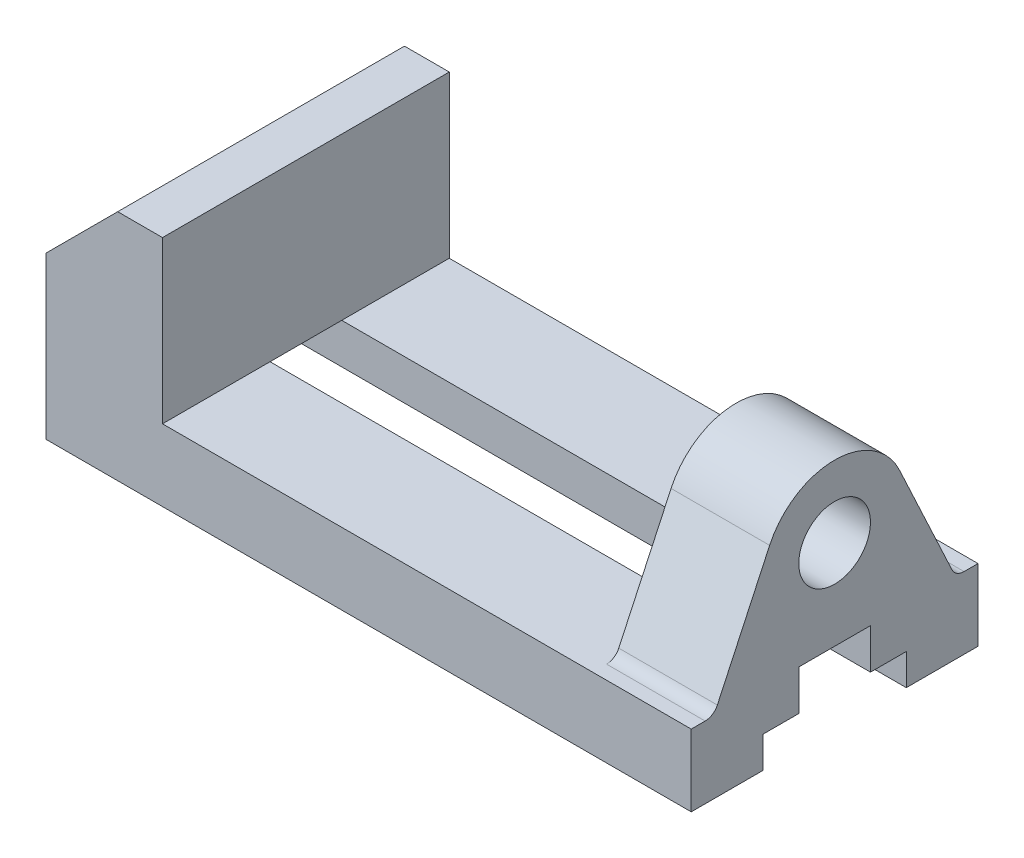
SolidWorks part; units mm, degrees
ref_plane "Front Plane" through (0, 0, 0) normal (0, 0, 1) x (1, 0, 0)
ref_plane "Top Plane" through (0, 0, 0) normal (0, 1, 0) x (1, 0, 0)
ref_plane "Right Plane" through (0, 0, 0) normal (1, 0, 0) x (0, 0, -1)
sketch "Sketch1" plane through (0, 0, 0) normal (0, 1, 0) x (1, 0, 0)
  line L1 (-72, 32) -> (72, 32)
  line L2 (-72, 32) -> (-72, -32)
  line L3 (-72, -32) -> (72, -32)
  line L4 (72, 32) -> (72, -32)
  line L5 (-72, 32) -> (72, -32) construction
  line L6 (-72, -32) -> (72, 32) construction
  point P0 (0, 0)
  dimension "D1" = 144
  dimension "D2" = 64
extrude "Boss-Extrude1" add sketch "Sketch1" against normal blind 16
sketch "Sketch2" plane through (72, 0, 0) normal (1, 0, 0) x (0, 0, -1)
  line L0 (0, 20.9312) -> (0, -20.9312) construction
  line L1 (-8, 0) -> (8, 0)
  line L2 (-32, 0) -> (32, 0) construction
  line L3 (8, 0) -> (8, -9)
  line L4 (-8, 0) -> (-8, -9)
  line L5 (8, -9) -> (16, -9)
  line L6 (-8, -9) -> (-16, -9)
  line L7 (16, -9) -> (16, -16)
  line L8 (-32, -16) -> (32, -16) construction
  line L9 (-16, -9) -> (-16, -16)
  line L10 (16, -16) -> (-16, -16)
  point P4 (0, 0)
  point P9 (0, 0)
  point P17 (0, -16)
  point P18 (8, -4.5)
  dimension "D1" = 32
  dimension "D2" = 7
  dimension "D3" = 16
extrude "Cut-Extrude1" cut sketch "Sketch2" against normal up to next
sketch "Sketch4" plane through (0, 0, 0) normal (0, 0, 1) x (1, 0, 0)
  line L0 (-72, 20) -> (-56, 36)
  line L1 (-72, 0) -> (-46, 0)
  line L2 (-72, 0) -> (-72, 20)
  line L3 (-56, 36) -> (-46, 36)
  line L4 (-46, 0) -> (-46, 36)
  point P2 (-72, 36)
  dimension "D1" = 10
  dimension "D2" = 36
extrude "Boss-Extrude2" add sketch "Sketch4" along normal mid plane 64
ref_plane "Plane1" through (72, 0, 0) normal (1, 0, 0) x (0, 0, -1)
sketch "Sketch5" plane through (72, 0, 0) normal (1, 0, 0) x (0, 0, -1)
  line L0 (26.9802, 0) -> (14.5009, 26.7619)
  line L1 (8, 0) -> (32, 0) construction
  line L2 (0, 20) -> (0, -8.5477) construction
  line L3 (-26.9802, 0) -> (-14.5009, 26.7619)
  line L4 (-32, 36) -> (32, 36) construction
  line L5 (26.9802, 0) -> (-26.9802, 0)
  circle A0 centre (0, 20) radius 8
  arc A1 (14.5009, 26.7619) -> (-14.5009, 26.7619) centre (0, 20) ccw
  dimension "D1" = 16
  dimension "D2" = 16
  dimension "D3" = 50
extrude "Boss-Extrude3" add sketch "Sketch5" against normal blind 22
fillet "Fillet1" radius 3 2 edges at (61, 0, 26.9802) (61, 0, -26.9802)
hole_wizard "Tap Drill for M6x1.0 Tap1" positions "Sketch7" profile "Sketch8" hole size "M6x1.0" standard "ANSI Metric"
sketch "Sketch7" plane through (0, -16, 0) normal (0, -1, 0) x (-1, 0, 0)
  line L8 (-100.9802, 0) -> (100.9802, 0) construction
  line L10 (0, 59.889) -> (0, -59.889) construction
  point P0 (35, 22)
  point P2 (-35, 22)
  point P4 (35, -22)
  point P6 (-35, -22)
  point P59 (0, 0)
  point P93 (0, 0)
  dimension "D1" = 70
  dimension "D2" = 44
sketch "Sketch8" plane through (-35, -16, -22) normal (1, 0, 0) x (0, 0, -1)
  line L0 (0, 0) -> (0, 10)
  line L1 (0, 10) -> (2.5, 8.4978)
  line L2 (2.5, 8.4978) -> (2.5, 0.025)
  line L3 (2.5, 0.025) -> (2.525, 0)
  line L5 (2.525, 0) -> (0, 0)
  line L6 (-2.5, 0.025) -> (-2.525, 0) construction
  line L10 (0, 10) -> (-2.5, 8.4978) construction
  line L11 (0, -6.35) -> (0, 107.95) construction
  dimension "Hole Dia." = 5
  dimension "Hole Depth" = 10
  dimension "Near C'Sink Dia." = 5.05
  dimension "Near C'Sink Angle" = 90
  dimension "Drill Angle" = 118
